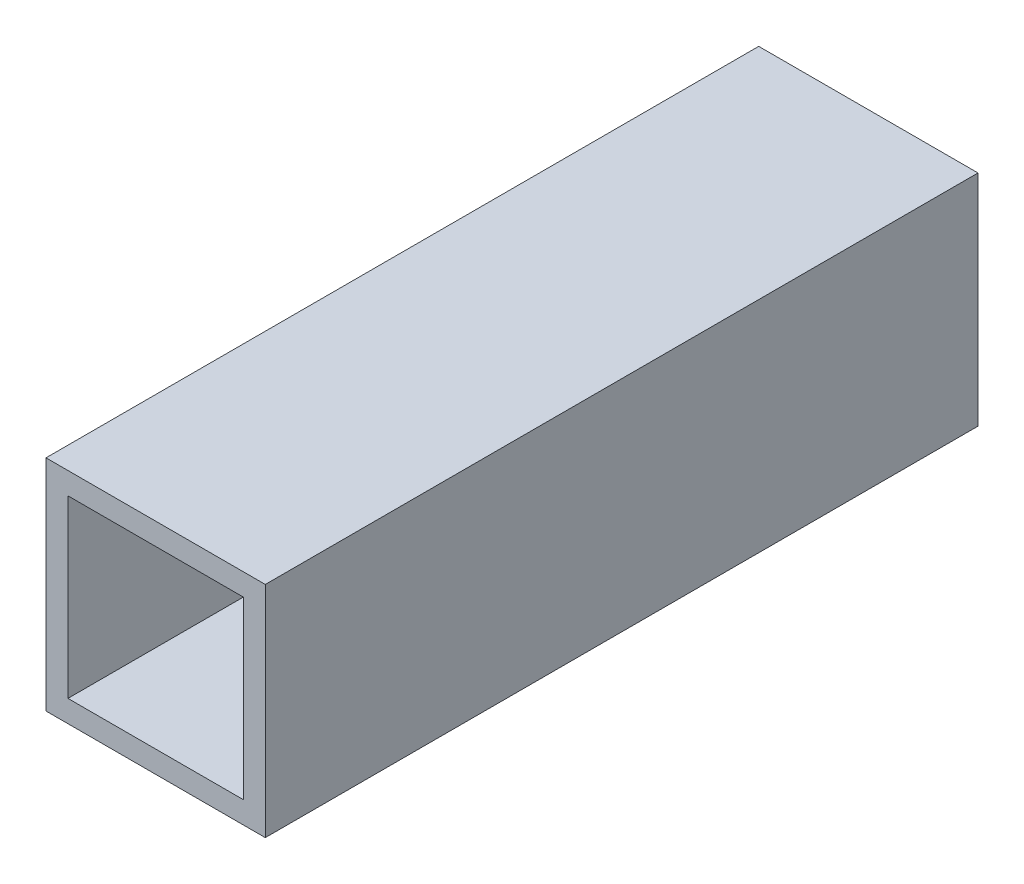
SolidWorks part; units mm, degrees
material "Alaşım Çelik"
ref_plane "Ön Düzlem" through (0, 0, 0) normal (0, 0, 1) x (1, 0, 0)
ref_plane "Üst Düzlem" through (0, 0, 0) normal (0, 1, 0) x (1, 0, 0)
ref_plane "Sağ Düzlem" through (0, 0, 0) normal (1, 0, 0) x (0, 0, -1)
sketch "Çizim1" plane through (0, 0, 0) normal (0, 0, 1) x (1, 0, 0)
  line L1 (0, 0) -> (40, 0)
  line L2 (0, 0) -> (0, 40)
  line L3 (0, 40) -> (40, 40)
  line L4 (40, 0) -> (40, 40)
  line L5 (4, 4) -> (36, 4)
  line L6 (4, 4) -> (4, 36)
  line L7 (4, 36) -> (36, 36)
  line L8 (36, 4) -> (36, 36)
  dimension "D1" = 40
  dimension "D2" = 40
  dimension "D3" = 32
  dimension "D4" = 32
  dimension "D5" = 4
  dimension "D6" = 4
extrude "Yükseklik-Ekstrüzyon1" add sketch "Çizim1" along normal blind 130
